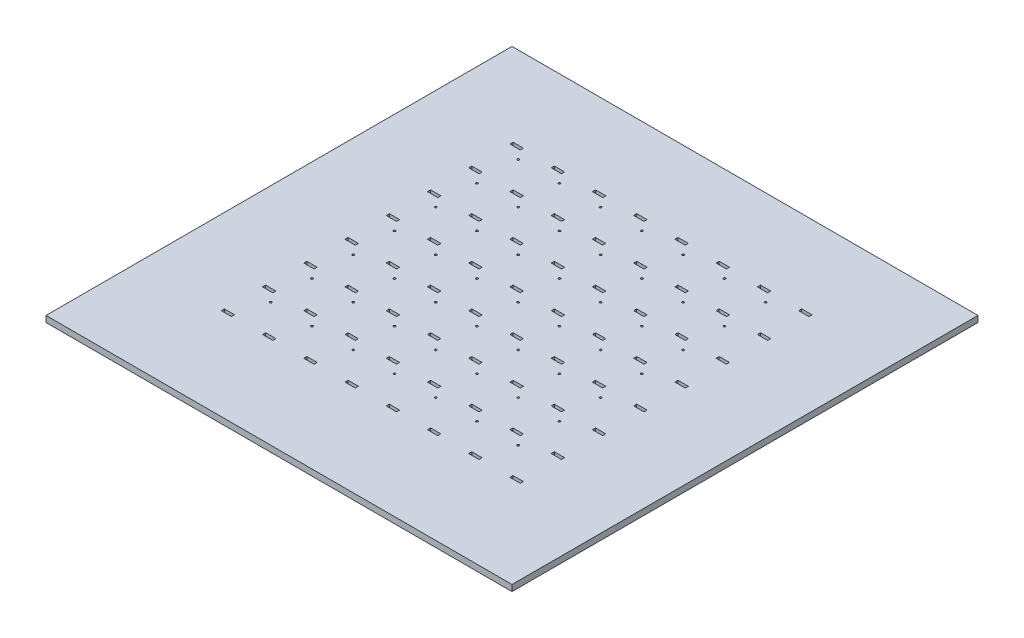
SolidWorks part; units mm, degrees
ref_plane "Plan de face" through (0, 0, 0) normal (0, 0, 1) x (1, 0, 0)
ref_plane "Plan de dessus" through (0, 0, 0) normal (0, 1, 0) x (1, 0, 0)
ref_plane "Plan de droite" through (0, 0, 0) normal (1, 0, 0) x (0, 0, -1)
sketch "Esquisse2" plane through (0, 0, 0) normal (0, 1, 0) x (1, 0, 0)
  line L1 (0, 0) -> (226, 0)
  line L2 (0, 0) -> (0, 226)
  line L3 (0, 226) -> (226, 226)
  line L4 (226, 0) -> (226, 226)
  dimension "D1" = 226
  dimension "D2" = 226
extrude "Boss.-Extru.1" add sketch "Esquisse2" along normal blind 3
sketch "Esquisse6" plane through (0, 3, 0) normal (0, 1, 0) x (1, 0, 0)
  line L0 (0, 226) -> (0, 0) construction
  line L1 (40.5, 184.5) -> (45.5, 184.5)
  line L2 (40.5, 184.5) -> (40.5, 186)
  line L3 (40.5, 186) -> (45.5, 186)
  line L4 (45.5, 184.5) -> (45.5, 186)
  line L5 (226, 226) -> (0, 226) construction
  dimension "D1" = 1.5
  dimension "D2" = 5
  dimension "D3" = 40.5
  dimension "D4" = 40
extrude "Enlèv. mat.-Extru.1" cut sketch "Esquisse6" against normal blind 5
pattern_linear "Répétition linéaire2" count 8 spacing 20 along (0, 0, 1) count 8 spacing 20 along (1, 0, 0) of "Enlèv. mat.-Extru.1"
sketch "Esquisse8" plane through (0, 3, 0) normal (0, 1, 0) x (1, 0, 0)
  line L0 (226, 226) -> (0, 226) construction
  line L1 (0, 226) -> (0, 0) construction
  circle A0 centre (49, 180) radius 0.5
  dimension "D1" = 1
  dimension "D2" = 46
  dimension "D3" = 49
extrude "Enlèv. mat.-Extru.2" cut sketch "Esquisse8" against normal blind 5
pattern_linear "Répétition linéaire3" count 7 spacing 20 along (0, 0, 1) count 7 spacing 20 along (1, 0, 0) of "Enlèv. mat.-Extru.2"
